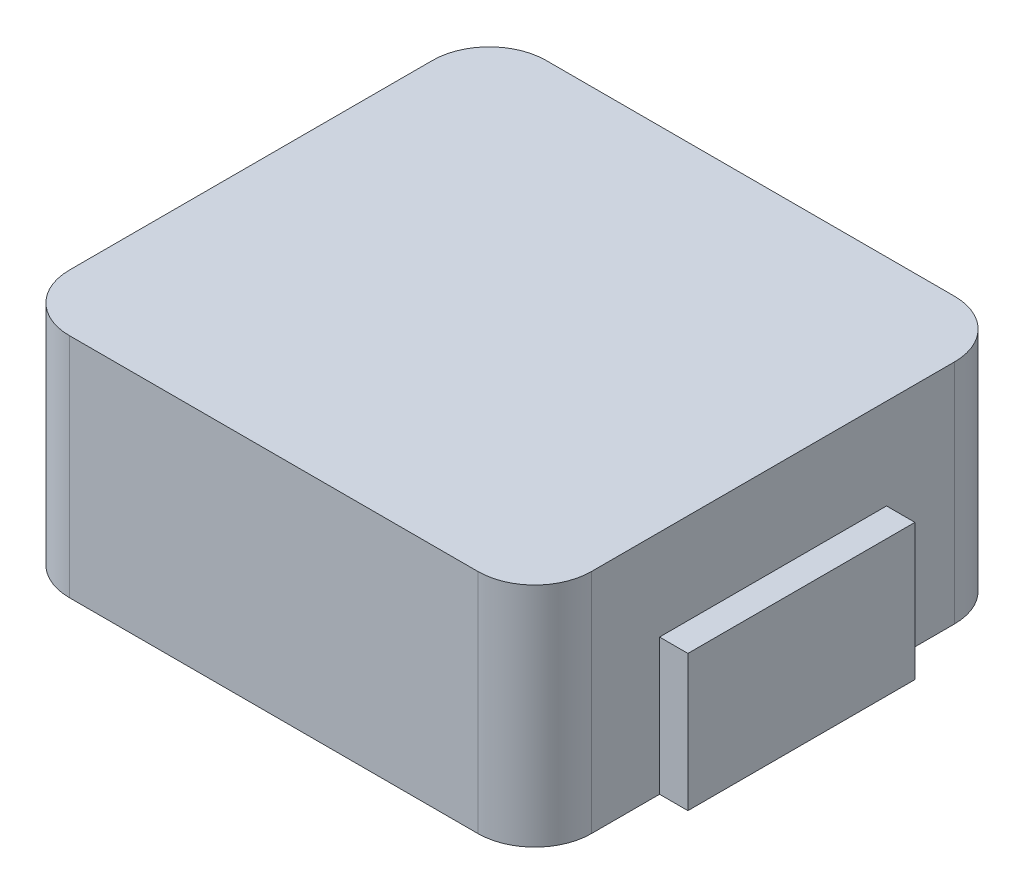
SolidWorks part; units mm, degrees
ref_plane "前视基准面" through (0, 0, 0) normal (0, 0, 1) x (1, 0, 0)
ref_plane "上视基准面" through (0, 0, 0) normal (0, 1, 0) x (1, 0, 0)
ref_plane "右视基准面" through (0, 0, 0) normal (1, 0, 0) x (0, 0, -1)
sketch "草图1" plane through (0, 0, 0) normal (0, 1, 0) x (1, 0, 0)
  line L1 (-2.3, -2.1) -> (2.3, -2.1)
  line L2 (-2.3, -2.1) -> (-2.3, 2.1)
  line L3 (-2.3, 2.1) -> (2.3, 2.1)
  line L4 (2.3, -2.1) -> (2.3, 2.1)
  line L5 (-2.3, -2.1) -> (2.3, 2.1) construction
  line L6 (-2.3, 2.1) -> (2.3, -2.1) construction
  point P0 (0, 0)
  dimension "D1" = 4.6
  dimension "D2" = 4.2
extrude "凸台-拉伸1" add sketch "草图1" along normal blind 2
fillet "圆角1" radius 0.5 4 edges at (-2.3, 1, -2.1) (2.3, 1, -2.1) (2.3, 1, 2.1) (-2.3, 1, 2.1)
sketch "草图2" plane through (0, 0, 0) normal (0, -1, 0) x (1, 0, 0)
  line L0 (0, -2.1) -> (0, 2.1) construction
  line L1 (1.8, -2.1) -> (-1.8, -2.1) construction
  line L2 (-1.8, 2.1) -> (1.8, 2.1) construction
  line L3 (0, 0) -> (2.3, 0) construction
  line L4 (2.3, 1.6) -> (2.3, -1.6) construction
  line L5 (-2.55, 1) -> (-2.55, -1)
  line L6 (2.05, 1) -> (2.55, 1)
  line L7 (2.05, 1) -> (2.05, -1)
  line L8 (2.05, -1) -> (2.55, -1)
  line L9 (2.55, 1) -> (2.55, -1)
  line L10 (2.05, 1) -> (2.55, -1) construction
  line L11 (2.05, -1) -> (2.55, 1) construction
  line L12 (-2.05, -1) -> (-2.55, -1)
  line L13 (-2.05, 1) -> (-2.05, -1)
  line L14 (-2.05, 1) -> (-2.55, 1)
  dimension "D1" = 2
  dimension "D2" = 0.5
extrude "凸台-拉伸2" add sketch "草图2" against normal blind 1.2
